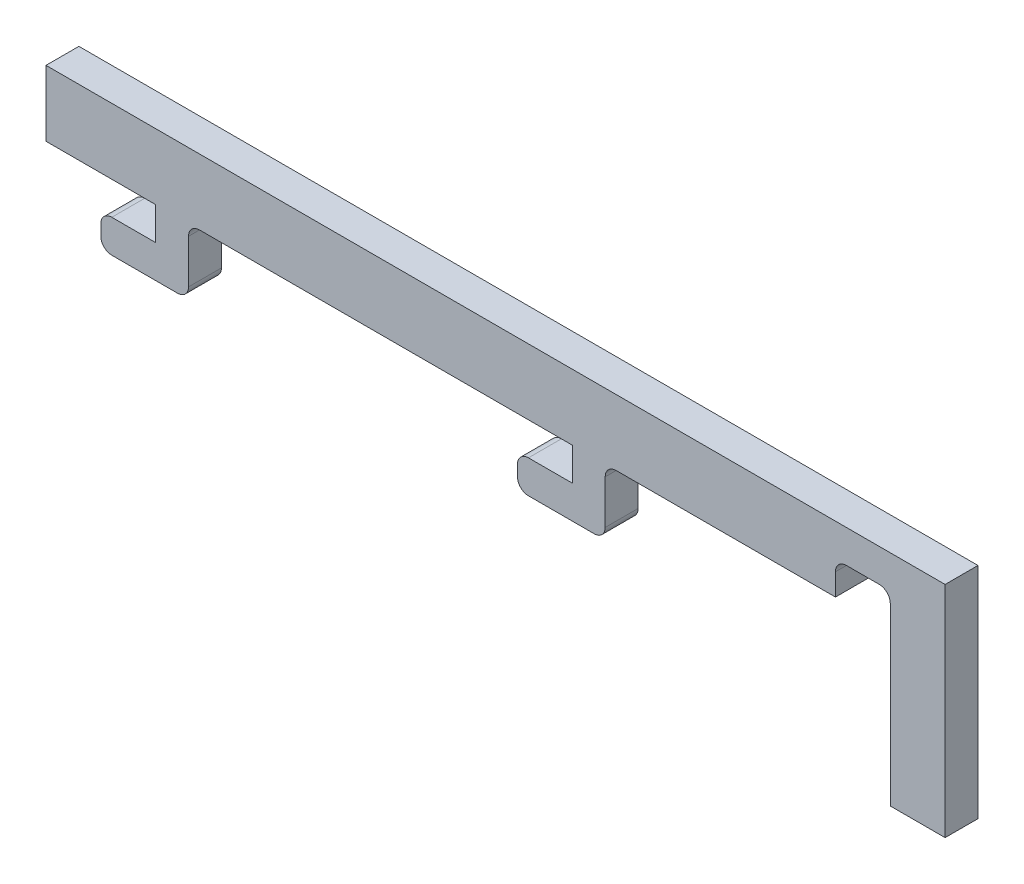
SolidWorks part; units mm, degrees
ref_plane "Front Plane" through (0, 0, 0) normal (0, 0, 1) x (1, 0, 0)
ref_plane "Top Plane" through (0, 0, 0) normal (0, 1, 0) x (1, 0, 0)
ref_plane "Right Plane" through (0, 0, 0) normal (1, 0, 0) x (0, 0, -1)
sketch "Sketch1" plane through (0, 0, 0) normal (0, 0, 1) x (1, 0, 0)
  line L0 (-29.3834, -8) -> (-35.3834, -8) construction
  line L1 (-35.3834, -5) -> (-31.3834, -5) construction
  line L2 (-31.3834, -5) -> (-31.3834, -2) construction
  line L3 (-31.3834, -2) -> (-41.3834, -2) construction
  line L4 (-41.3834, -2) -> (-41.3834, 1) construction
  line L5 (35.6166, 4) -> (40.6166, 4) construction
  line L6 (40.6166, 4) -> (40.6166, -16) construction
  line L7 (40.6166, -16) -> (35.6166, -16) construction
  line L8 (35.6166, -16) -> (35.6166, 0) construction
  line L9 (30.6166, -2) -> (10.6166, -2) construction
  line L10 (8.6166, -8) -> (2.6166, -8) construction
  line L11 (2.6166, -5) -> (6.6166, -5) construction
  line L12 (6.6166, -5) -> (6.6166, -2) construction
  line L13 (-28.3834, -7) -> (-28.3834, -3) construction
  line L14 (-27.3834, -2) -> (6.6166, -2) construction
  line L15 (9.6166, -7) -> (9.6166, -3) construction
  line L16 (29.6166, 4) -> (35.6166, 4) construction
  line L17 (1.6166, -6) -> (1.6166, -7) construction
  line L18 (-36.3834, -6) -> (-36.3834, -7) construction
  line L19 (29.6166, 4) -> (-41.3834, 4) construction
  line L20 (-41.3834, 4) -> (-41.3834, 1) construction
  line L21 (30.6166, 0) -> (30.6166, -2) construction
  line L22 (31.6166, 1) -> (34.6166, 1) construction
  arc A0 (-36.3834, -7) -> (-35.3834, -8) centre (-35.3834, -7) ccw construction
  arc A1 (-35.3834, -5) -> (-36.3834, -6) centre (-35.3834, -6) ccw construction
  arc A2 (35.6166, 0) -> (34.6166, 1) centre (34.6166, 0) ccw construction
  arc A3 (10.6166, -2) -> (9.6166, -3) centre (10.6166, -3) ccw construction
  arc A4 (1.6166, -7) -> (2.6166, -8) centre (2.6166, -7) ccw construction
  arc A5 (2.6166, -5) -> (1.6166, -6) centre (2.6166, -6) ccw construction
  arc A6 (-29.3834, -8) -> (-28.3834, -7) centre (-29.3834, -7) ccw construction
  arc A7 (-27.3834, -2) -> (-28.3834, -3) centre (-27.3834, -3) ccw construction
  arc A8 (8.6166, -8) -> (9.6166, -7) centre (8.6166, -7) ccw construction
  arc A9 (31.6166, 1) -> (30.6166, 0) centre (31.6166, 0) ccw construction
sketch "Sketch3" plane through (0, 0, 0) normal (0, 0, 1) x (1, 0, 0)
  line L0 (29.6166, 4) -> (-41.3834, 4) construction
  line L1 (-41.3834, 4) -> (-41.3834, 1) construction
  line L2 (-41.3834, -2) -> (-41.3834, 1) construction
  line L3 (-31.3834, -2) -> (-41.3834, -2) construction
  line L4 (-31.3834, -5) -> (-31.3834, -2) construction
  line L5 (-35.3834, -5) -> (-31.3834, -5) construction
  line L6 (-36.3834, -6) -> (-36.3834, -7) construction
  line L7 (-29.3834, -8) -> (-35.3834, -8) construction
  line L8 (-28.3834, -7) -> (-28.3834, -3) construction
  line L9 (-27.3834, -2) -> (6.6166, -2) construction
  line L10 (6.6166, -5) -> (6.6166, -2) construction
  line L11 (2.6166, -5) -> (6.6166, -5) construction
  line L12 (1.6166, -6) -> (1.6166, -7) construction
  line L13 (8.6166, -8) -> (2.6166, -8) construction
  line L14 (9.6166, -7) -> (9.6166, -3) construction
  line L15 (30.6166, -2) -> (10.6166, -2) construction
  line L16 (30.6166, 0) -> (30.6166, -2) construction
  line L17 (31.6166, 1) -> (34.6166, 1) construction
  line L18 (35.6166, -16) -> (35.6166, 0) construction
  line L19 (40.6166, -16) -> (35.6166, -16) construction
  line L20 (40.6166, 4) -> (40.6166, -16) construction
  line L21 (35.6166, 4) -> (40.6166, 4) construction
  line L22 (29.6166, 4) -> (35.6166, 4) construction
  line L23 (29.6166, 4) -> (-41.3834, 4)
  line L24 (-41.3834, 4) -> (-41.3834, 1)
  line L25 (-41.3834, -2) -> (-41.3834, 1)
  line L26 (-31.3834, -2) -> (-41.3834, -2)
  line L27 (-31.3834, -5) -> (-31.3834, -2)
  line L28 (-35.3834, -5) -> (-31.3834, -5)
  line L29 (-36.3834, -6) -> (-36.3834, -7)
  line L30 (-29.3834, -8) -> (-35.3834, -8)
  line L31 (-28.3834, -7) -> (-28.3834, -3)
  line L32 (-27.3834, -2) -> (6.6166, -2)
  line L33 (6.6166, -5) -> (6.6166, -2)
  line L34 (2.6166, -5) -> (6.6166, -5)
  line L35 (1.6166, -6) -> (1.6166, -7)
  line L36 (8.6166, -8) -> (2.6166, -8)
  line L37 (9.6166, -7) -> (9.6166, -3)
  line L38 (30.6166, -2) -> (10.6166, -2)
  line L39 (30.6166, 0) -> (30.6166, -2)
  line L40 (31.6166, 1) -> (34.6166, 1)
  line L41 (35.6166, -16) -> (35.6166, 0)
  line L42 (40.6166, -16) -> (35.6166, -16)
  line L43 (40.6166, 4) -> (40.6166, -16)
  line L44 (35.6166, 4) -> (40.6166, 4)
  line L45 (29.6166, 4) -> (35.6166, 4)
  arc A0 (-35.3834, -5) -> (-36.3834, -6) centre (-35.3834, -6) ccw construction
  arc A1 (-36.3834, -7) -> (-35.3834, -8) centre (-35.3834, -7) ccw construction
  arc A2 (-29.3834, -8) -> (-28.3834, -7) centre (-29.3834, -7) ccw construction
  arc A3 (-27.3834, -2) -> (-28.3834, -3) centre (-27.3834, -3) ccw construction
  arc A4 (2.6166, -5) -> (1.6166, -6) centre (2.6166, -6) ccw construction
  arc A5 (1.6166, -7) -> (2.6166, -8) centre (2.6166, -7) ccw construction
  arc A6 (8.6166, -8) -> (9.6166, -7) centre (8.6166, -7) ccw construction
  arc A7 (10.6166, -2) -> (9.6166, -3) centre (10.6166, -3) ccw construction
  arc A8 (31.6166, 1) -> (30.6166, 0) centre (31.6166, 0) ccw construction
  arc A9 (35.6166, 0) -> (34.6166, 1) centre (34.6166, 0) ccw construction
  arc A10 (-35.3834, -5) -> (-36.3834, -6) centre (-35.3834, -6) ccw
  arc A11 (-36.3834, -7) -> (-35.3834, -8) centre (-35.3834, -7) ccw
  arc A12 (-29.3834, -8) -> (-28.3834, -7) centre (-29.3834, -7) ccw
  arc A13 (-27.3834, -2) -> (-28.3834, -3) centre (-27.3834, -3) ccw
  arc A14 (2.6166, -5) -> (1.6166, -6) centre (2.6166, -6) ccw
  arc A15 (1.6166, -7) -> (2.6166, -8) centre (2.6166, -7) ccw
  arc A16 (8.6166, -8) -> (9.6166, -7) centre (8.6166, -7) ccw
  arc A17 (10.6166, -2) -> (9.6166, -3) centre (10.6166, -3) ccw
  arc A18 (31.6166, 1) -> (30.6166, 0) centre (31.6166, 0) ccw
  arc A19 (35.6166, 0) -> (34.6166, 1) centre (34.6166, 0) ccw
extrude "Boss-Extrude1" add sketch "Sketch3" along normal blind 3
